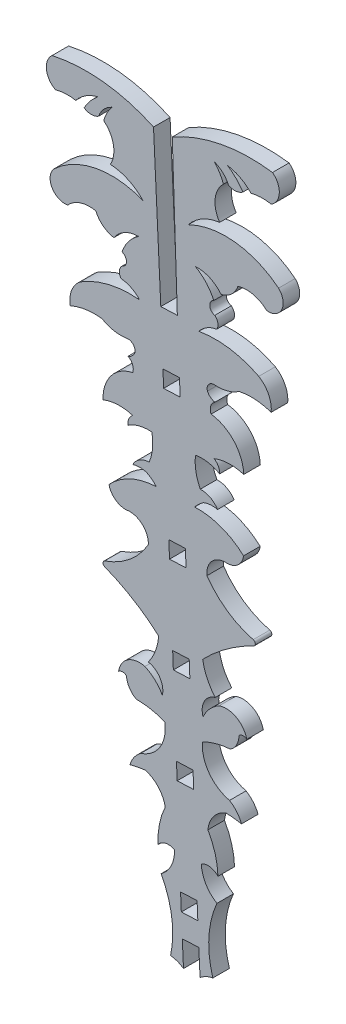
SolidWorks part; units mm, degrees
ref_plane "Front Plane" through (0, 0, 0) normal (0, 0, 1) x (1, 0, 0)
ref_plane "Top Plane" through (0, 0, 0) normal (0, 1, 0) x (1, 0, 0)
ref_plane "Right Plane" through (0, 0, 0) normal (1, 0, 0) x (0, 0, -1)
sketch "Sketch1" plane through (0, 0, 0) normal (0, 0, 1) x (1, 0, 0)
  line L0 (104.0994, 66.0852) -> (104.7701, 52.1028)
  line L2 (105.5107, 33.8862) -> (107.0335, 33.9481)
  line L3 (105.5315, 52.1337) -> (103.7618, 89.0248) construction
  line L5 (107.651, 0) -> (107.2696, 0)
  line L6 (107.651, 0) -> (108.0312, 0.031)
  line L8 (105.8264, 66.1554) -> (106.2929, 52.1647)
  line L10 (104.7701, 52.1028) -> (106.2929, 52.1647)
  line L11 (107.7377, 16.6263) -> (107.7996, 15.1036)
  line L12 (104.9681, 47.2337) -> (106.4908, 47.2956)
  line L13 (105.03, 45.711) -> (106.5527, 45.7729)
  line L14 (106.4908, 47.2956) -> (106.5527, 45.7729)
  line L15 (104.9681, 47.2337) -> (105.03, 45.711)
  line L16 (105.5726, 32.3634) -> (107.0954, 32.4253)
  line L18 (106.2769, 15.0416) -> (107.7996, 15.1036)
  line L19 (106.215, 16.5644) -> (106.2769, 15.0416)
  line L20 (105.5107, 33.8862) -> (105.5726, 32.3634)
  line L21 (107.0335, 33.9481) -> (107.0954, 32.4253)
  line L22 (106.215, 16.5644) -> (107.7377, 16.6263)
  line L24 (105.9248, 23.7025) -> (107.4475, 23.7645)
  line L25 (105.8628, 25.2253) -> (107.3856, 25.2872)
  line L26 (105.9248, 23.7025) -> (105.8628, 25.2253)
  line L27 (107.4475, 23.7645) -> (107.3856, 25.2872)
  arc A0 (104.0994, 66.0852) -> (94.7554, 67.1137) centre (97.9184, 52.8915) ccw
  arc A1 (94.7554, 67.1137) -> (95.0768, 64.5431) centre (95.7998, 65.9389) ccw
  arc A2 (95.0768, 64.5431) -> (96.9408, 64.6325) centre (96.1992, 60.6184) cw
  arc A3 (96.9408, 64.6325) -> (98.997, 65.9389) centre (99.8513, 62.3228) cw
  arc A4 (98.997, 65.9389) -> (97.7109, 64.4196) centre (101.963, 62.1242) ccw
  arc A5 (97.7109, 64.4196) -> (99.0425, 64.4196) centre (98.3767, 65.4497) ccw
  arc A6 (99.0425, 64.4196) -> (100.2584, 65.7439) centre (101.197, 63.6619) cw
  arc A7 (100.2584, 65.7439) -> (99.5147, 64.3038) centre (103.3094, 63.2562) ccw
  arc A8 (99.5147, 64.3038) -> (100.1272, 61.1194) centre (97.942, 62.3502) cw
  arc A9 (100.1272, 61.1194) -> (103.1317, 59.7305) centre (99.9242, 56.7363) cw
  arc A10 (103.1317, 59.7305) -> (94.9238, 58.1566) centre (100.2615, 52.5097) ccw
  arc A11 (94.9238, 58.1566) -> (96.1992, 55.9142) centre (95.9394, 57.2503) ccw
  arc A12 (96.1992, 55.9142) -> (98.7981, 56.7363) centre (98.2056, 54.0903) cw
  arc A13 (98.7981, 56.7363) -> (100.4499, 55.4432) centre (100.7917, 57.5813) ccw
  arc A14 (100.4499, 55.4432) -> (102.7234, 56.6755) centre (102.7572, 53.9001) cw
  arc A15 (102.7234, 56.6755) -> (101.197, 54.6791) centre (104.9114, 53.421) ccw
  arc A16 (101.197, 54.6791) -> (101.197, 53.5401) centre (101.0097, 54.1096) cw
  arc A17 (101.197, 53.5401) -> (101.1051, 52.5097) centre (101.7103, 52.975) ccw
  arc A18 (101.1051, 52.5097) -> (102.8196, 51.6591) centre (100.8842, 49.9111) cw
  arc A19 (102.8196, 51.6591) -> (97.3879, 50.3854) centre (101.992, 42.9696) ccw
  arc A20 (97.3879, 50.3854) -> (96.4354, 48.0006) centre (98.816, 48.4324) ccw
  arc A21 (96.4354, 48.0006) -> (99.3466, 48.4324) centre (98.6702, 42.9639) cw
  arc A22 (99.3466, 48.4324) -> (101.6092, 48.0006) centre (101.0939, 51.4436) ccw
  arc A23 (101.6092, 48.0006) -> (102.3867, 47.2337) centre (101.7541, 47.37) cw
  arc A24 (102.3867, 47.2337) -> (101.7541, 46.634) centre (101.4294, 47.61) cw
  arc A25 (101.7541, 46.634) -> (102.1832, 45.5505) centre (101.3552, 45.8493) cw
  arc A26 (102.1832, 45.5505) -> (99.457, 42.009) centre (102.9246, 42.1597) ccw
  arc A27 (99.457, 42.009) -> (102.1832, 42.1275) centre (100.9875, 38.2154) cw
  arc A28 (102.1832, 42.1275) -> (101.7541, 41.1273) centre (102.8034, 41.2693) ccw
  arc A29 (101.7541, 41.1273) -> (103.9436, 41.6867) centre (103.6259, 38.366) cw
  arc A30 (103.9436, 41.6867) -> (103.7026, 39.1677) centre (99.7153, 40.8203) cw
  arc A31 (103.7026, 39.1677) -> (102.1832, 38.2154) centre (103.7661, 37.3782) ccw
  arc A32 (102.1832, 38.2154) -> (103.4968, 38.2154) centre (102.84, 36.1713) cw
  arc A33 (103.4968, 38.2154) -> (104.3618, 37.5336) centre (101.8304, 35.2119) cw
  arc A34 (104.3618, 37.5336) -> (99.9992, 35.5316) centre (104.5778, 31.3086) ccw
  arc A35 (99.9992, 35.5316) -> (101.8304, 34.3308) centre (101.5221, 35.8572) ccw
  arc A36 (101.8304, 34.3308) -> (103.6259, 32.5499) centre (101.9026, 32.608) cw
  arc A37 (103.6259, 32.5499) -> (99.6218, 29.2425) centre (97.2079, 36.2423) cw
  arc A38 (99.6122, 28.7658) -> (104.5778, 25.7324) centre (93.5661, 13.2873) cw
  arc A39 (99.6218, 29.2425) -> (99.6122, 28.7658) centre (99.7046, 29.0023) ccw
  arc A40 (104.5778, 25.7324) -> (103.6259, 23.1882) centre (99.5547, 26.1615) cw
  arc A41 (103.6259, 23.1882) -> (104.9114, 21.1776) centre (103.3039, 21.566) cw
  arc A42 (104.9114, 21.1776) -> (103.3039, 22.6733) centre (101.9005, 19.5533) ccw
  arc A43 (103.3039, 22.6733) -> (100.8842, 21.066) centre (102.8062, 20.7974) ccw
  arc A44 (100.8842, 21.066) -> (101.6092, 21.066) centre (101.2467, 20.6945) cw
  arc A45 (101.6092, 21.066) -> (102.5072, 19.6637) centre (103.3516, 21.1931) ccw
  arc A46 (102.5072, 19.6637) -> (105.1366, 19.1697) centre (102.5533, 12.6642) cw
  arc A47 (105.1366, 19.1697) -> (102.9246, 15.5537) centre (101.9301, 18.6467) cw
  arc A48 (102.9246, 15.5537) -> (101.9301, 14.1498) centre (104.5197, 13.3697) ccw
  arc A49 (101.9301, 14.1498) -> (103.3516, 14.4197) centre (104.5799, 4.0731) cw
  arc A50 (103.3516, 14.4197) -> (105.179, 12.3859) centre (102.6251, 11.9291) cw
  arc A51 (105.179, 12.3859) -> (104.5197, 9.0792) centre (111.3877, 9.4288) ccw
  arc A52 (104.5197, 9.0792) -> (106.0335, 9.4288) centre (105.4927, 8.3182) cw
  arc A53 (106.0335, 9.4288) -> (104.7963, 6.8879) centre (103.038, 9.3156) cw
  arc A54 (104.7963, 6.8879) -> (105.6677, 0.7976) centre (97.0316, 2.6695) cw
  arc A55 (105.6677, 0.7976) -> (107.2696, 0) centre (105.4287, -1.6897) cw
  arc A56 (109.563, 0.956) -> (108.0312, 0.031) centre (110.0031, -1.5038) ccw
  arc A57 (109.9371, 7.0969) -> (109.563, 0.956) centre (118.0187, 3.5227) ccw
  arc A58 (108.4978, 9.529) -> (109.9371, 7.0969) centre (111.4926, 9.6594) ccw
  arc A59 (110.035, 9.3034) -> (108.4978, 9.529) centre (109.127, 8.4659) ccw
  arc A60 (109.1094, 12.5457) -> (110.035, 9.3034) centre (103.1613, 9.0944) cw
  arc A61 (110.7657, 14.7211) -> (109.1094, 12.5457) centre (111.6919, 12.2977) ccw
  arc A62 (112.2044, 14.5675) -> (110.7657, 14.7211) centre (110.3814, 4.309) ccw
  arc A63 (111.0992, 15.8861) -> (112.2044, 14.5675) centre (109.6867, 13.5798) cw
  arc A64 (108.601, 19.3105) -> (111.0992, 15.8861) centre (111.8393, 19.0495) ccw
  arc A65 (111.1816, 20.0163) -> (108.601, 19.3105) centre (111.7039, 13.0362) ccw
  arc A66 (111.9629, 21.487) -> (111.1816, 20.0163) centre (110.2159, 21.4722) cw
  arc A67 (112.6854, 21.5458) -> (111.9629, 21.487) centre (112.3543, 21.1461) ccw
  arc A68 (110.1433, 22.9513) -> (112.6854, 21.5458) centre (110.7916, 21.1221) cw
  arc A69 (108.6624, 21.3301) -> (110.1433, 22.9513) centre (111.7952, 19.9555) cw
  arc A70 (109.7805, 23.4384) -> (108.6624, 21.3301) centre (110.2332, 21.8477) ccw
  arc A71 (108.6253, 25.897) -> (109.7805, 23.4384) centre (113.5969, 26.7324) ccw
  arc A72 (113.28, 29.7977) -> (113.3282, 29.3234) centre (113.2169, 29.5517) cw
  arc A73 (113.3282, 29.3234) -> (108.6253, 25.897) centre (120.6108, 14.3868) ccw
  arc A74 (109.0206, 32.7693) -> (113.28, 29.7977) centre (115.1177, 36.9704) ccw
  arc A75 (110.6656, 34.69) -> (109.0206, 32.7693) centre (110.7335, 32.9671) ccw
  arc A76 (112.3932, 36.0355) -> (110.6656, 34.69) centre (110.849, 36.2364) cw
  arc A77 (107.8826, 37.6767) -> (112.3932, 36.0355) centre (108.1726, 31.4547) cw
  arc A78 (108.6893, 38.4265) -> (107.8826, 37.6767) centre (110.594, 35.5682) ccw
  arc A79 (109.9986, 38.5331) -> (108.6893, 38.4265) centre (109.5099, 36.4425) ccw
  arc A80 (108.4069, 39.359) -> (109.9986, 38.5331) centre (108.4889, 37.5702) cw
  arc A81 (107.9622, 41.8501) -> (108.4069, 39.359) centre (112.2469, 41.3297) ccw
  arc A82 (110.1899, 41.4702) -> (107.9622, 41.8501) centre (108.5485, 38.5662) ccw
  arc A83 (109.681, 42.4323) -> (110.1899, 41.4702) centre (109.1326, 41.5266) cw
  arc A84 (112.4079, 42.5355) -> (109.681, 42.4323) centre (111.1903, 38.6302) ccw
  arc A85 (109.4032, 45.844) -> (112.4079, 42.5355) centre (108.9395, 42.4042) cw
  arc A86 (109.7429, 46.9588) -> (109.4032, 45.844) centre (110.2042, 46.2091) ccw
  arc A87 (109.0637, 47.5052) -> (109.7429, 46.9588) centre (109.9873, 47.958) ccw
  arc A88 (109.7764, 48.3326) -> (109.0637, 47.5052) centre (109.6831, 47.6923) ccw
  arc A89 (111.9964, 48.9467) -> (109.7764, 48.3326) centre (110.0105, 51.8062) cw
  arc A90 (114.9331, 48.7526) -> (111.9964, 48.9467) centre (113.1145, 43.5511) ccw
  arc A91 (113.7902, 51.0522) -> (114.9331, 48.7526) centre (112.5253, 48.9898) cw
  arc A92 (108.273, 51.8808) -> (113.7902, 51.0522) centre (109.8032, 43.2872) cw
  arc A93 (109.9128, 52.8678) -> (108.273, 51.8808) centre (110.3439, 50.2957) ccw
  arc A94 (109.7375, 53.8873) -> (109.9128, 52.8678) centre (109.2718, 53.2824) cw
  arc A95 (109.645, 55.0225) -> (109.7375, 53.8873) centre (109.878, 54.4701) ccw
  arc A96 (107.9616, 56.8885) -> (109.645, 55.0225) centre (106.045, 53.4671) cw
  arc A97 (110.3276, 55.8448) -> (107.9616, 56.8885) centre (108.1533, 54.1195) ccw
  arc A98 (111.8691, 57.2677) -> (110.3276, 55.8448) centre (109.8135, 57.9481) cw
  arc A99 (114.5261, 56.6593) -> (111.8691, 57.2677) centre (112.6744, 54.6786) ccw
  arc A100 (115.6153, 58.9978) -> (114.5261, 56.6593) centre (114.6766, 58.0121) cw
  arc A101 (107.3068, 59.9002) -> (115.6153, 58.9978) centre (110.7536, 52.9362) cw
  arc A102 (110.1885, 61.5285) -> (107.3068, 59.9002) centre (110.7467, 57.1762) ccw
  arc A103 (110.5406, 64.752) -> (110.1885, 61.5285) centre (112.2667, 62.9325) ccw
  arc A104 (109.6824, 66.1271) -> (110.5406, 64.752) centre (106.8434, 63.3999) cw
  arc A105 (111.0017, 64.9058) -> (109.6824, 66.1271) centre (108.9158, 63.9757) ccw
  arc A106 (112.329, 65.0139) -> (111.0017, 64.9058) centre (111.5818, 65.9865) cw
  arc A107 (110.9238, 66.4238) -> (112.329, 65.0139) centre (108.2773, 62.3809) cw
  arc A108 (113.0792, 65.2887) -> (110.9238, 66.4238) centre (110.3658, 62.7502) ccw
  arc A109 (114.9444, 65.3508) -> (113.0792, 65.2887) centre (114.1443, 61.348) ccw
  arc A110 (115.056, 67.9391) -> (114.9444, 65.3508) centre (114.1105, 66.6833) cw
  arc A111 (105.8264, 66.1554) -> (115.056, 67.9391) centre (113.0579, 53.507) cw
  point P115 (104.7701, 52.1028)
  point P232 (106.8896, -0.031)
  point P233 (106.2929, 52.1647)
  point P234 (108.4124, 0.031)
  dimension "D1" = 0.254
  dimension "D2" = 1.524
  dimension "D3" = 1.524
extrude "Boss-Extrude1" add sketch "Sketch1" along normal blind 1.524
sketch "Sketch2" plane through (0, 0, 1.524) normal (0, 0, 1) x (1, 0, 0)
  line L0 (107.6611, -0.4201) -> (107.5097, 2.7118) construction
  line L1 (108.4222, -0.3833) -> (108.2709, 2.7486)
  line L2 (106.8999, -0.4568) -> (106.7486, 2.675)
  line L3 (108.4222, -0.3833) -> (106.8999, -0.4568)
  line L4 (108.2709, 2.7486) -> (106.7486, 2.675)
  line L5 (106.5895, 6.3356) -> (106.6576, 4.7695)
  line L6 (107.3507, 6.3687) -> (107.4188, 4.8026) construction
  line L7 (108.112, 6.4018) -> (108.1801, 4.8357)
  line L8 (106.5895, 6.3356) -> (108.112, 6.4018)
  line L9 (106.6576, 4.7695) -> (108.1801, 4.8357)
  dimension "D1" = 0.762
  dimension "D2" = 0.762
  dimension "D3" = 0.762
  dimension "D4" = 0.762
extrude "Cut-Extrude1" cut sketch "Sketch2" against normal blind 1.524
